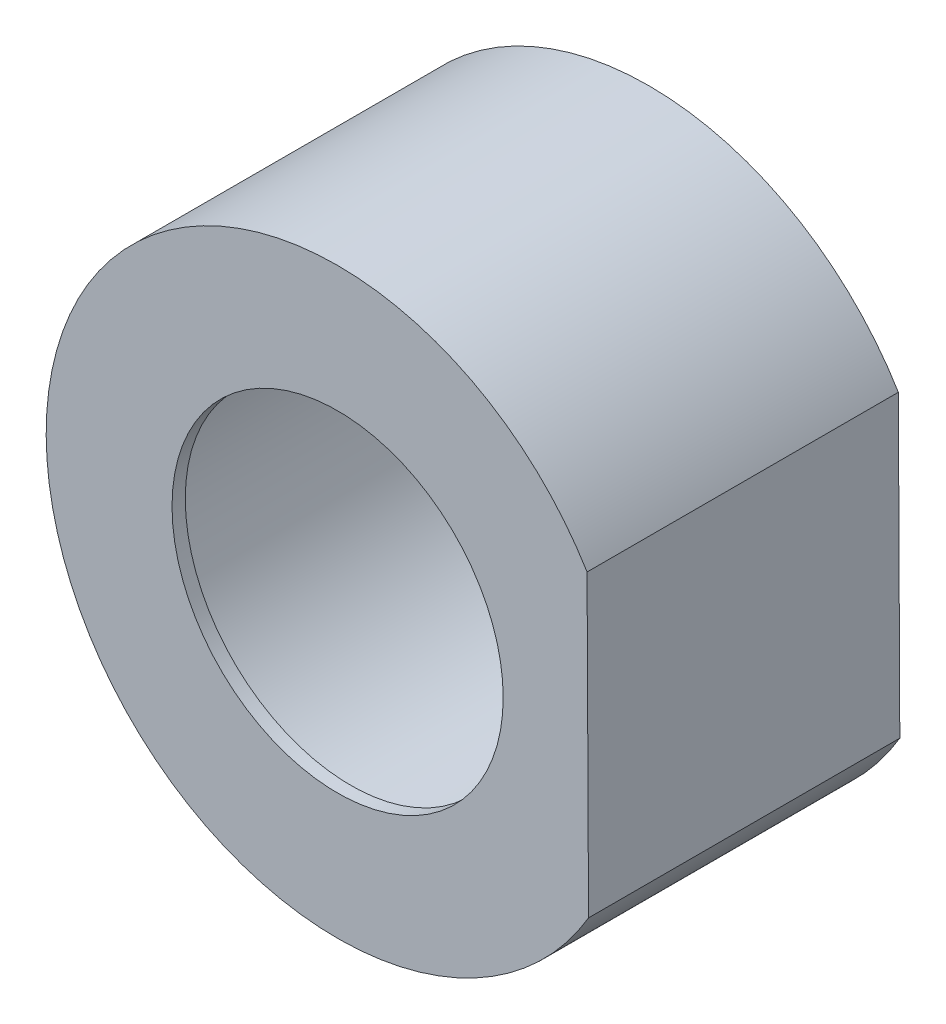
SolidWorks part; units mm, degrees
ref_plane "Спереди" through (0, 0, 0) normal (0, 0, 1) x (1, 0, 0)
ref_plane "Сверху" through (0, 0, 0) normal (0, 1, 0) x (1, 0, 0)
ref_plane "Справа" through (0, 0, 0) normal (1, 0, 0) x (0, 0, -1)
sketch "Эскиз1" plane through (0, 0, 0) normal (0, 0, 1) x (1, 0, 0)
  line L0 (18.943, -11.1875) -> (18.8327, 11.3724)
  arc A0 (18.8327, 11.3724) -> (18.943, -11.1875) centre (0, 0) ccw
extrude "Вытянуть1" add sketch "Эскиз1" along normal blind 23.5
ref_plane "Плоскость1" through (0, 0, 12.5) normal (0, 0, 1) x (1, 0, 0)
sketch "Эскиз6" plane through (0, 0, 0) normal (0, 0, -1) x (-1, 0, 0)
  circle A0 centre (0, 0) radius 16
extrude "Вытянуть8" cut sketch "Эскиз6" against normal blind 22.5
sketch "Эскиз7" plane through (0, 0, 22.5) normal (0, 0, -1) x (-1, 0, 0)
  circle A0 centre (0, 0) radius 12.5
extrude "Вытянуть9" cut sketch "Эскиз7" against normal through all
